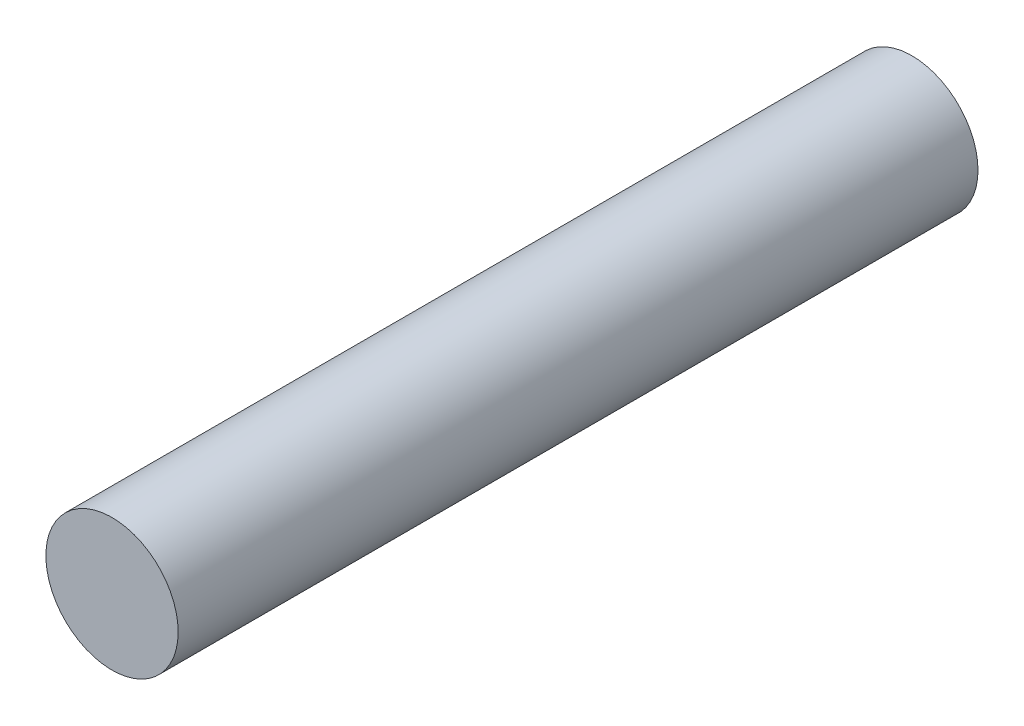
SolidWorks part; units mm, degrees
ref_plane "Alzado" through (0, 0, 0) normal (0, 0, 1) x (1, 0, 0)
ref_plane "Planta" through (0, 0, 0) normal (0, 1, 0) x (1, 0, 0)
ref_plane "Vista lateral" through (0, 0, 0) normal (1, 0, 0) x (0, 0, -1)
sketch "Croquis1" plane through (0, 0, 0) normal (0, 0, 1) x (1, 0, 0)
  circle A0 centre (0, 0) radius 2.15
  dimension "D1" = 4.3
extrude "Saliente-Extruir1" add sketch "Croquis1" along normal blind 26
